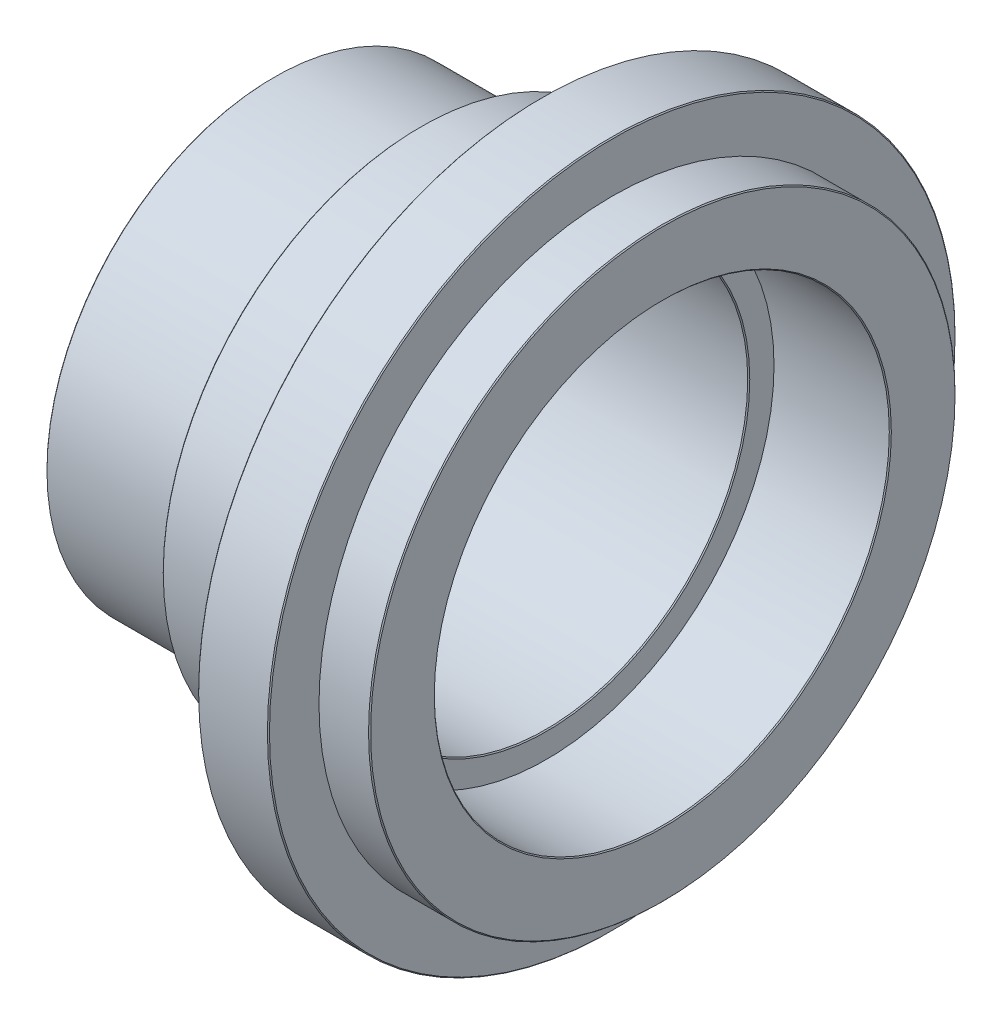
SolidWorks part; units mm, degrees
ref_plane "Plan de face" through (0, 0, 0) normal (0, 0, 1) x (1, 0, 0)
ref_plane "Plan de dessus" through (0, 0, 0) normal (0, 1, 0) x (1, 0, 0)
ref_plane "Plan de droite" through (0, 0, 0) normal (1, 0, 0) x (0, 0, -1)
sketch "Esquisse1" plane through (0, 0, 0) normal (0, 0, 1) x (1, 0, 0)
  line L0 (0, 0) -> (-64.1281, 0) construction
  line L1 (0, 45) -> (0, 58)
  line L2 (0, 58) -> (-10, 58)
  line L3 (-10, 58) -> (-10, 68)
  line L4 (-10, 68) -> (-24, 68)
  line L5 (-24, 68) -> (-24, 56.1962)
  line L6 (-27, 51) -> (-48, 51)
  line L7 (-48, 51) -> (-48, 45)
  line L8 (-48, 45) -> (-77, 45)
  line L9 (-77, 45) -> (-77, 40)
  line L10 (-77, 40) -> (-23, 40)
  line L11 (-23, 40) -> (-23, 45)
  line L12 (-23, 45) -> (0, 45)
  line L13 (-24, 56.1962) -> (-27, 51)
  point P3 (-5, 58)
  point P9 (-24, 51)
  dimension "D1" = 24
  dimension "D2" = 48
  dimension "D3" = 77
  dimension "D4" = 10
  dimension "D5" = 23
  dimension "D6" = 90
  dimension "D7" = 116
  dimension "D8" = 136
  dimension "D9" = 102
  dimension "D10" = 90
  dimension "D11" = 40
  dimension "D12" = 3
  dimension "D13" = 60
revolve "Révolution1" add sketch "Esquisse1" angle 360 about L0
chamfer "Chanfrein1" distance 0.2 angle 45 7 edges at (0, 0, -45) (0, 0, -58) (-10, 0, -68) (-24, 0, -68) (-48, 0, -51) (-77, 0, -40) (-77, 0, -45)
chamfer "Chanfrein2" distance 0.2 angle 45 1 edges at (-23, 0, -40)
